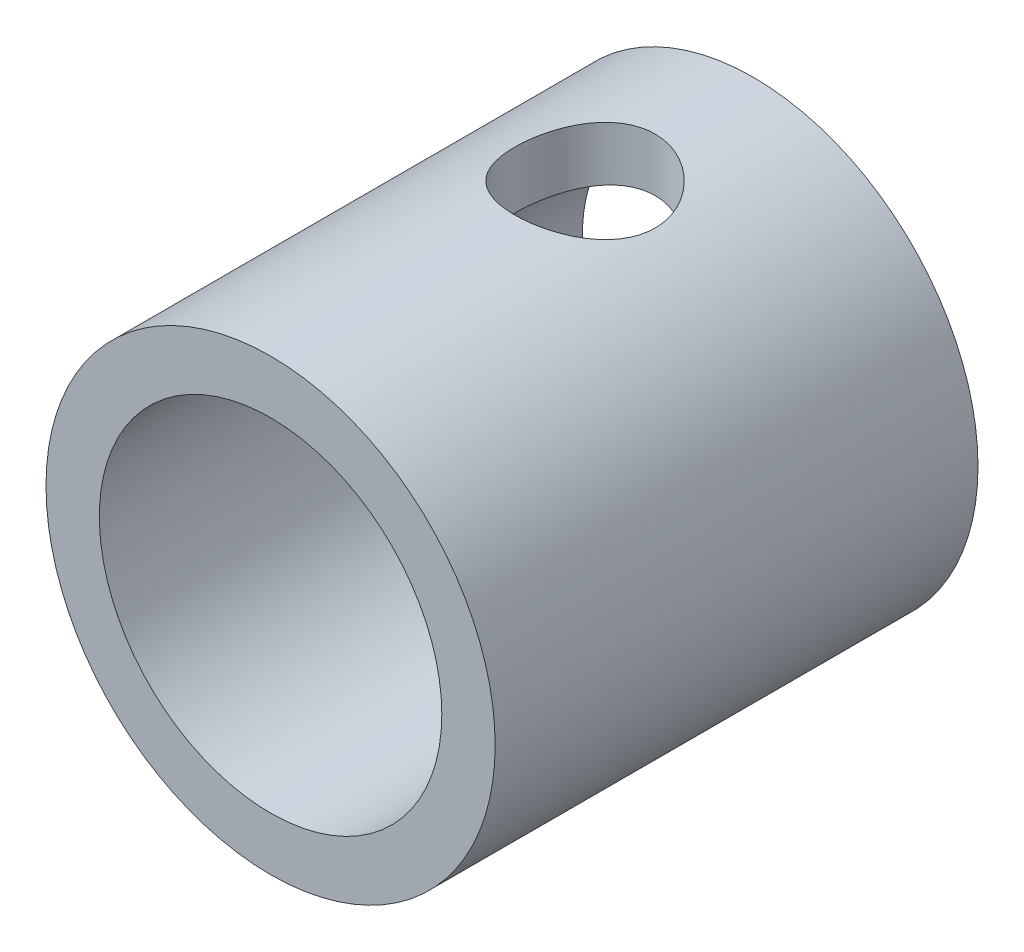
SolidWorks part; units mm, degrees
material "Unlegierter Baustahl"
ref_plane "Ebene vorne" through (0, 0, 0) normal (0, 0, 1) x (1, 0, 0)
ref_plane "Ebene oben" through (0, 0, 0) normal (0, 1, 0) x (1, 0, 0)
ref_plane "Ebene rechts" through (0, 0, 0) normal (1, 0, 0) x (0, 0, -1)
sketch "Skizze2" plane through (0, 0, 0) normal (0, 0, 1) x (1, 0, 0)
  circle A0 centre (0, 0) radius 3.05
  circle A1 centre (0, 0) radius 4
  dimension "D1" = 6.1
  dimension "D2" = 8
extrude "Aufsatz-Linear austragen1" add sketch "Skizze2" against normal mid plane 8.6
sketch "Skizze3" plane through (0, 0, 0) normal (0, 1, 0) x (1, 0, 0)
  line L0 (0, 1.3) -> (0, 4.3) construction
  line L1 (3.05, 4.3) -> (-3.05, 4.3) construction
  circle A0 centre (0, 1.3) radius 1.25
  dimension "D1" = 2.5
  dimension "D2" = 3
extrude "Schnitt-Linear austragen1" cut sketch "Skizze3" along normal through all
